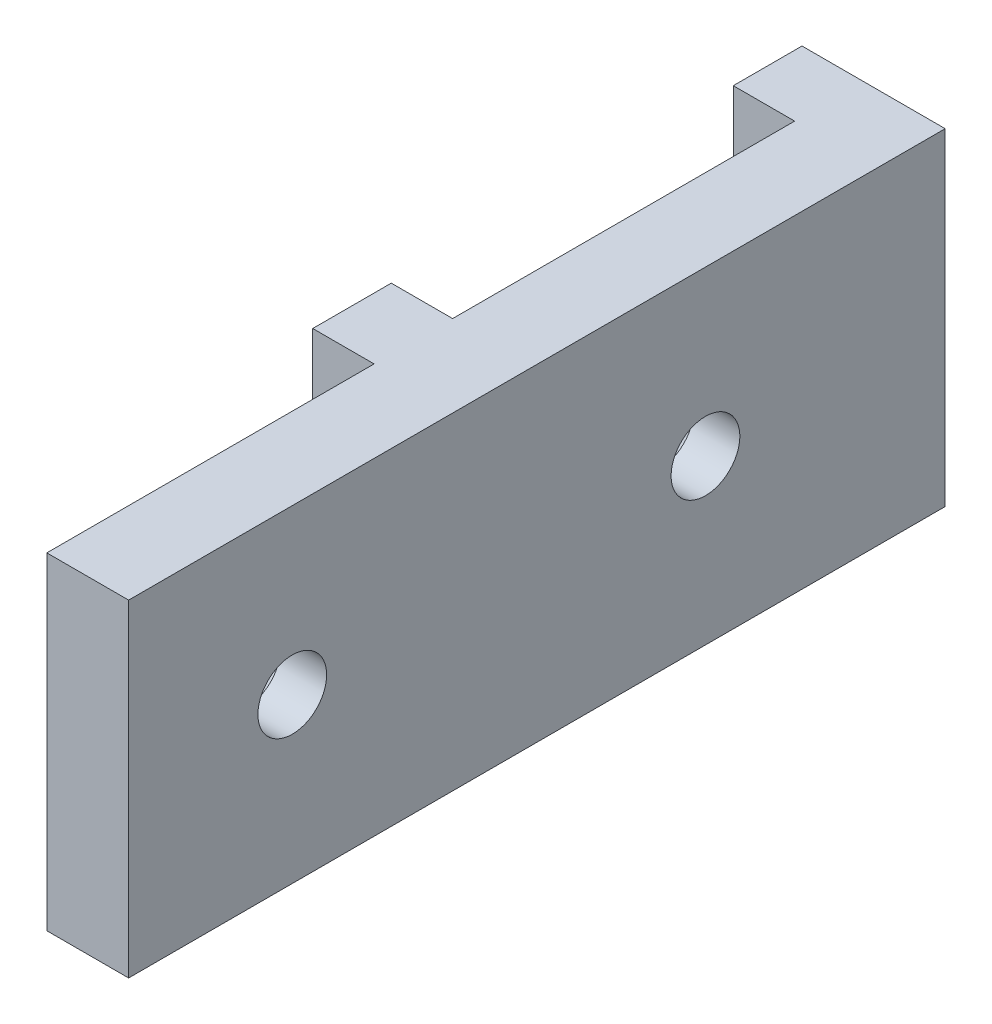
SolidWorks part; units mm, degrees
ref_plane "Front" through (0, 0, 0) normal (0, 0, 1) x (1, 0, 0)
ref_plane "Top" through (0, 0, 0) normal (0, 1, 0) x (1, 0, 0)
ref_plane "Right" through (0, 0, 0) normal (1, 0, 0) x (0, 0, -1)
sketch "Sketch1" plane through (0, 0, 0) normal (1, 0, 0) x (0, 0, -1)
  line L1 (0, 0) -> (6.096, 0)
  line L2 (0, 0) -> (0, 25.4)
  line L3 (0, 25.4) -> (6.096, 25.4)
  line L4 (6.096, 0) -> (6.096, 25.4)
  line L5 (0, 0) -> (6.096, 25.4) construction
  line L6 (0, 25.4) -> (6.096, 0) construction
  point P4 (3.048, 12.7)
  dimension "D1" = 25.4
  dimension "D2" = 6.096
extrude "Boss-Extrude1" add sketch "Sketch1" along normal blind 4.7625
sketch "Sketch2" plane through (4.7625, 0, 0) normal (1, 0, 0) x (0, 0, -1)
  line L0 (0, 25.4) -> (6.096, 0) construction
  line L2 (-31.877, 0) -> (37.973, 0)
  line L3 (-31.877, 0) -> (-31.877, 25.4)
  line L4 (-31.877, 25.4) -> (37.973, 25.4)
  line L5 (37.973, 0) -> (37.973, 25.4)
  line L6 (-31.877, 0) -> (37.973, 25.4) construction
  line L7 (-31.877, 25.4) -> (37.973, 0) construction
  point P4 (3.048, 12.7)
  dimension "D1" = 69.85
extrude "Boss-Extrude2" add sketch "Sketch2" along normal blind 6.35
sketch "Sketch5" plane through (4.7625, 0, 0) normal (-1, 0, 0) x (0, 0, 1)
  line L5 (-6.096, 0) -> (-37.973, 0) construction
  line L6 (-37.973, 25.4) -> (-32.639, 25.4)
  line L14 (-37.973, 25.4) -> (-37.973, 0)
  line L15 (-37.973, 0) -> (-32.639, 0)
  line L16 (-32.639, 25.4) -> (-32.639, 0)
  line L17 (-37.973, 25.4) -> (-32.639, 0) construction
  line L18 (-37.973, 0) -> (-32.639, 25.4) construction
  point P4 (-35.306, 12.7)
  dimension "D1" = 5.334
extrude "Boss-Extrude3" add sketch "Sketch5" along normal blind 4.7625
sketch "Sketch6" plane through (4.7625, 0, 0) normal (-1, 0, 0) x (0, 0, 1)
  line L0 (31.877, 0) -> (0, 0) construction
  line L1 (31.877, 25.4) -> (25.4, 25.4)
  line L2 (31.877, 25.4) -> (31.877, 0)
  line L3 (31.877, 0) -> (25.4, 0)
  line L4 (25.4, 25.4) -> (25.4, 0)
  line L5 (31.877, 25.4) -> (25.4, 0) construction
  line L6 (31.877, 0) -> (25.4, 25.4) construction
  line L7 (0, 25.4) -> (0, 0) construction
  point P4 (28.6385, 12.7)
  dimension "D1" = 25.4
extrude "Cut-Extrude3" cut sketch "Sketch6" against normal up to next
sketch "Sketch3" plane through (4.7625, 0, 0) normal (-1, 0, 0) x (0, 0, 1)
  line L0 (-19.3675, 25.4) -> (-19.3675, 0) construction
  line L1 (-32.639, 25.4) -> (-6.096, 25.4) construction
  line L2 (-6.096, 0) -> (-32.639, 0) construction
  line L3 (12.7, 25.4) -> (12.7, 0) construction
  line L4 (0, 25.4) -> (25.4, 25.4) construction
  line L5 (25.4, 0) -> (0, 0) construction
  circle A0 centre (-19.3675, 12.7) radius 2.667
  circle A1 centre (12.7, 12.7) radius 2.667
  dimension "D1" = 5.334
extrude "Cut-Extrude1" cut sketch "Sketch3" against normal up to next
sketch "Sketch4" plane through (4.7625, 0, 0) normal (-1, 0, 0) x (0, 0, 1)
  circle A1 centre (12.7, 12.7) radius 4.7625
  circle A3 centre (-19.3675, 12.7) radius 4.7625
  dimension "D1" = 9.525
extrude "Cut-Extrude2" cut sketch "Sketch4" against normal blind 3.81 draft 37
